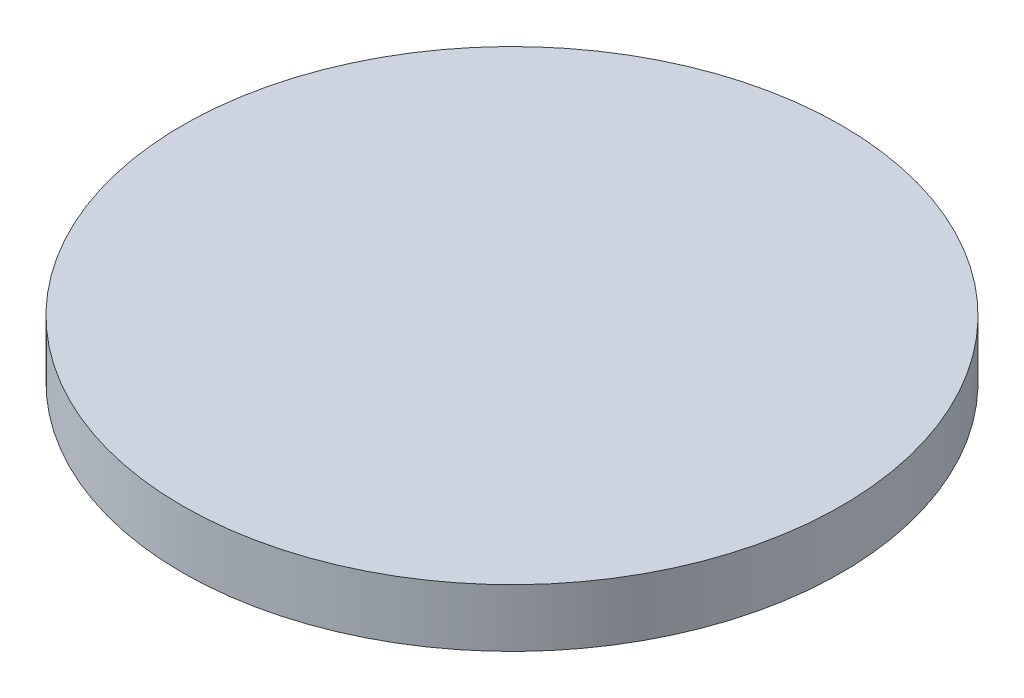
SolidWorks part; units mm, degrees
material "Balsa"
ref_plane "Front Plane" through (0, 0, 0) normal (0, 0, 1) x (1, 0, 0)
ref_plane "Top Plane" through (0, 0, 0) normal (0, 1, 0) x (1, 0, 0)
ref_plane "Right Plane" through (0, 0, 0) normal (1, 0, 0) x (0, 0, -1)
sketch "Sketch1" plane through (0, 0, 0) normal (0, 1, 0) x (1, 0, 0)
  circle A0 centre (0, 0) radius 36.195
  dimension "D1" = 72.39
extrude "Boss-Extrude1" add sketch "Sketch1" along normal blind 6.35
